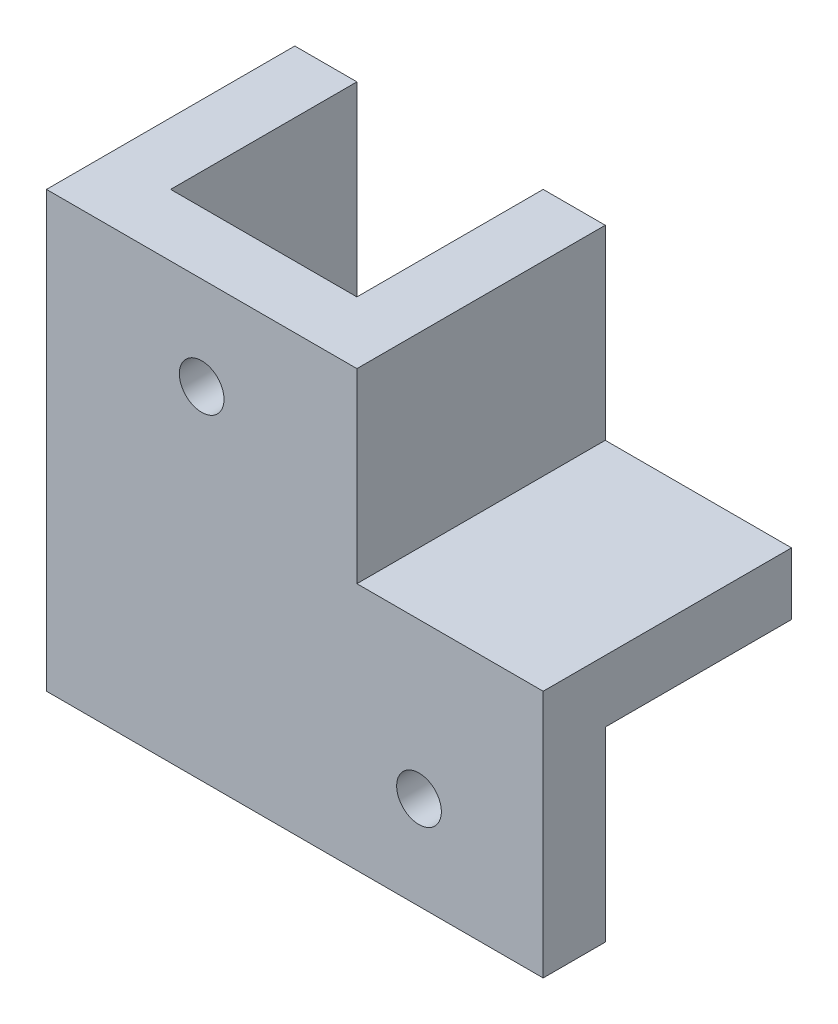
SolidWorks part; units mm, degrees
ref_plane "前视基准面" through (0, 0, 0) normal (0, 0, 1) x (1, 0, 0)
ref_plane "上视基准面" through (0, 0, 0) normal (0, 1, 0) x (1, 0, 0)
ref_plane "右视基准面" through (0, 0, 0) normal (1, 0, 0) x (0, 0, -1)
sketch "Sketch1" plane through (0, 0, 0) normal (0, 0, 1) x (1, 0, 0)
  line L0 (-7.5299, -25.8068) -> (27.4701, -25.8068)
  line L3 (-7.5299, 9.1932) -> (7.4701, 9.1932)
  line L4 (-7.5299, 9.1932) -> (-7.5299, -25.8068)
  line L6 (7.4701, 9.1932) -> (7.4701, -10.8068)
  line L7 (27.4701, -25.8068) -> (27.4701, -10.8068)
  line L8 (27.4701, -10.8068) -> (7.4701, -10.8068)
  dimension "D1" = 15
  dimension "D2" = 35
  dimension "D3" = 35
  dimension "D4" = 15
extrude "Boss-Extrude1" add sketch "Sketch1" along normal blind 5
sketch "Sketch2" plane through (0, 0, 0) normal (0, 0, -1) x (-1, 0, 0)
  line L0 (-7.4701, 9.1932) -> (-12.4701, 9.1932)
  line L1 (-12.4701, 9.1932) -> (-12.4701, -5.8068)
  line L2 (-12.4701, -5.8068) -> (-27.4701, -5.8068)
  line L3 (-27.4701, -10.8068) -> (-27.4701, -5.8068)
  line L4 (-27.4701, -10.8068) -> (-7.4701, -10.8068)
  line L5 (-7.4701, -10.8068) -> (-7.4701, 9.1932)
  dimension "D1" = 5
  dimension "D2" = 5
extrude "Boss-Extrude2" add sketch "Sketch2" along normal blind 15 separate body
sketch "Sketch3" plane through (0, 0, 0) normal (0, 0, -1) x (-1, 0, 0)
  line L0 (7.5299, 9.1932) -> (12.5299, 9.1932)
  line L1 (7.5299, -25.8068) -> (12.5299, -25.8068)
  line L2 (12.5299, -25.8068) -> (12.5299, 9.1932)
  line L3 (7.5299, -25.8068) -> (7.5299, 9.1932)
  dimension "D1" = 5
extrude "Boss-Extrude3" add sketch "Sketch3" along normal blind 15 separate body
sketch "Sketch4" plane through (0, 0, 0) normal (0, 0, 1) x (1, 0, 0)
  line L1 (-12.5299, 9.1932) -> (-7.5299, 9.1932)
  line L2 (-12.5299, 9.1932) -> (-12.5299, -25.8068)
  line L3 (-12.5299, -25.8068) -> (-7.5299, -25.8068)
  line L4 (-7.5299, 9.1932) -> (-7.5299, -25.8068)
extrude "Boss-Extrude4" add sketch "Sketch4" along normal blind 5
sketch "Sketch5" plane through (0, 0, 0) normal (0, 0, 1) x (1, 0, 0)
  line L0 (7.4701, 9.1932) -> (7.4701, -10.8068)
  line L1 (7.4701, -10.8068) -> (27.4701, -10.8068)
  line L2 (27.4701, -10.8068) -> (27.4701, -5.8068)
  line L3 (27.4701, -5.8068) -> (12.4701, -5.8068)
  line L4 (12.4701, -5.8068) -> (12.4701, 9.1932)
  line L5 (12.4701, 9.1932) -> (7.4701, 9.1932)
extrude "Boss-Extrude5" add sketch "Sketch5" along normal blind 5
sketch "Sketch7" plane through (0, 0, 0) normal (0, 0, -1) x (-1, 0, 0)
  line L0 (-27.4701, -25.8068) -> (-27.4701, -10.8068) construction
  line L1 (-27.4701, -10.8068) -> (-7.4701, -10.8068) construction
  line L2 (-7.4701, 9.1932) -> (7.5299, 9.1932) construction
  line L3 (7.5299, 9.1932) -> (7.5299, -25.8068) construction
  circle A0 centre (0.0299, 1.6932) radius 1.8
  circle A1 centre (-17.4701, -18.3068) radius 1.8
  dimension "D1" = 3.6
  dimension "D2" = 3.6
  dimension "D3" = 10
  dimension "D5" = 7.5
  dimension "D6" = 7.5
  dimension "D4" = 7.5
extrude "Cut-Extrude1" cut sketch "Sketch7" against normal through all
sketch "Sketch8" plane through (0, 0, -15) normal (0, 0, -1) x (-1, 0, 0)
  line L0 (12.5299, 9.1932) -> (-12.4701, 9.1932)
  line L1 (-12.4701, 9.1932) -> (-12.4701, -5.8068)
  line L2 (-12.4701, -5.8068) -> (-27.4701, -5.8068)
  line L3 (-27.4701, -5.8068) -> (-27.4701, -10.8068) construction
  line L4 (-27.4701, -5.8068) -> (-27.4701, -25.8068)
  line L5 (-27.4701, -25.8068) -> (12.5299, -25.8068)
  line L6 (12.5299, -25.8068) -> (12.5299, 9.1932)
